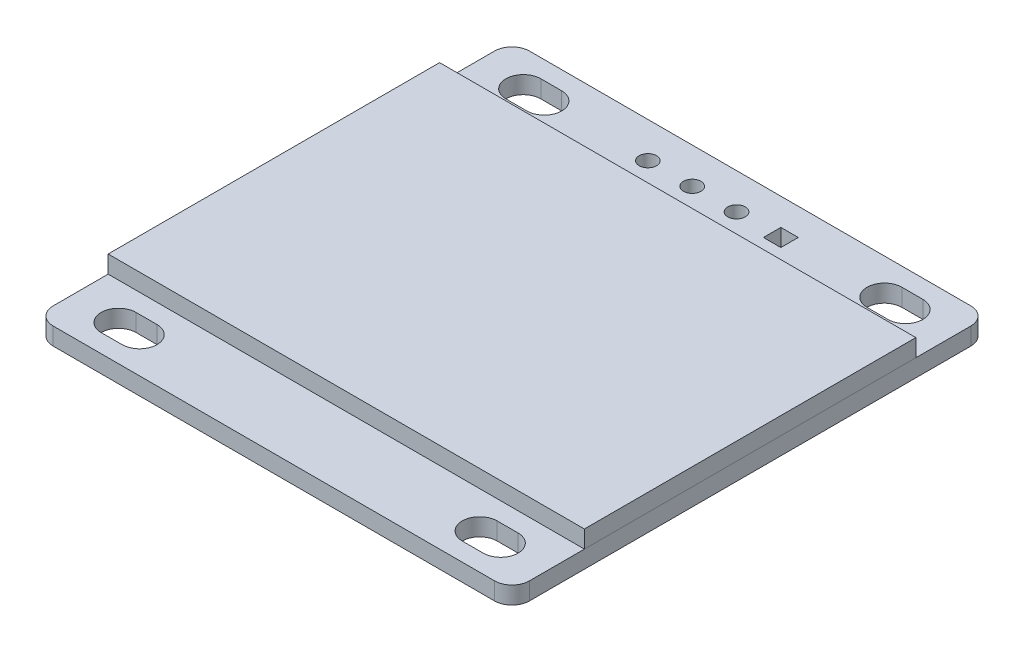
SolidWorks part; units mm, degrees
ref_plane "Přední rovina" through (0, 0, 0) normal (0, 0, 1) x (1, 0, 0)
ref_plane "Vrchní rovina" through (0, 0, 0) normal (0, 1, 0) x (1, 0, 0)
ref_plane "Pravá rovina" through (0, 0, 0) normal (1, 0, 0) x (0, 0, -1)
sketch "Skica1" plane through (0, 0, 0) normal (0, 1, 0) x (1, 0, 0)
  line L1 (0, 0) -> (27.3, 0)
  line L2 (0, 0) -> (0, 27.3)
  line L3 (0, 27.3) -> (27.3, 27.3)
  line L4 (27.3, 0) -> (27.3, 27.3)
  dimension "D1" = 27.3
  dimension "D2" = 27.3
extrude "Přidat vysunutím1" add sketch "Skica1" along normal blind 1
sketch "Skica2" plane through (0, 1, 0) normal (0, 1, 0) x (1, 0, 0)
  line L0 (0, 13.65) -> (27.3, 13.65) construction
  line L1 (0, 27.3) -> (0, 0) construction
  line L2 (27.3, 0) -> (27.3, 27.3) construction
  line L4 (0, 4.15) -> (27.3, 4.15)
  line L5 (0, 4.15) -> (0, 23.15)
  line L6 (0, 23.15) -> (27.3, 23.15)
  line L7 (27.3, 4.15) -> (27.3, 23.15)
  line L8 (0, 4.15) -> (27.3, 23.15) construction
  line L9 (0, 23.15) -> (27.3, 4.15) construction
  point P6 (13.65, 13.65)
  dimension "D1" = 19
extrude "Přidat vysunutím2" add sketch "Skica2" along normal blind 1 separate body
sketch "Skica3" plane through (0, 1, 0) normal (0, 1, 0) x (1, 0, 0)
  line L0 (0, 13.65) -> (27.3, 13.65) construction
  line L1 (0, 27.3) -> (0, 0) construction
  line L2 (27.3, 4.15) -> (27.3, 23.15) construction
  line L3 (13.65, 27.3) -> (13.65, 0) construction
  line L4 (27.3, 27.3) -> (0, 27.3) construction
  line L5 (0, 0) -> (27.3, 0) construction
  line L6 (0, 25.25) -> (27.3, 25.25) construction
  line L7 (27.3, 0) -> (27.3, 27.3) construction
  line L8 (3.3, 27.3) -> (3.3, 23.15) construction
  line L9 (27.3, 23.15) -> (0, 23.15) construction
  line L10 (2.7, 25.25) -> (3.9, 25.25) construction
  line L11 (2.7, 26.25) -> (3.9, 26.25)
  line L12 (2.7, 24.25) -> (3.9, 24.25)
  line L13 (24.6, 25.25) -> (23.4, 25.25) construction
  line L14 (24.6, 26.25) -> (23.4, 26.25)
  line L15 (24.6, 24.25) -> (23.4, 24.25)
  line L16 (2.7, 2.05) -> (3.9, 2.05) construction
  line L17 (2.7, 1.05) -> (3.9, 1.05)
  line L18 (2.7, 3.05) -> (3.9, 3.05)
  line L19 (24.6, 2.05) -> (23.4, 2.05) construction
  line L20 (24.6, 1.05) -> (23.4, 1.05)
  line L21 (24.6, 3.05) -> (23.4, 3.05)
  line L23 (16.96, 24.75) -> (17.96, 24.75)
  line L24 (16.96, 24.75) -> (16.96, 25.75)
  line L25 (16.96, 25.75) -> (17.96, 25.75)
  line L26 (17.96, 24.75) -> (17.96, 25.75)
  line L27 (16.96, 24.75) -> (17.96, 25.75) construction
  line L28 (16.96, 25.75) -> (17.96, 24.75) construction
  arc A0 (2.7, 26.25) -> (2.7, 24.25) centre (2.7, 25.25) ccw
  arc A1 (3.9, 24.25) -> (3.9, 26.25) centre (3.9, 25.25) ccw
  arc A2 (24.6, 26.25) -> (24.6, 24.25) centre (24.6, 25.25) cw
  arc A3 (23.4, 24.25) -> (23.4, 26.25) centre (23.4, 25.25) cw
  arc A4 (2.7, 1.05) -> (2.7, 3.05) centre (2.7, 2.05) cw
  arc A5 (3.9, 3.05) -> (3.9, 1.05) centre (3.9, 2.05) cw
  arc A6 (24.6, 1.05) -> (24.6, 3.05) centre (24.6, 2.05) ccw
  arc A7 (23.4, 3.05) -> (23.4, 1.05) centre (23.4, 2.05) ccw
  circle A8 centre (9.84, 25.25) radius 0.5
  circle A9 centre (12.38, 25.25) radius 0.5
  circle A10 centre (14.92, 25.25) radius 0.5
  point P22 (3.3, 25.25)
  point P31 (17.46, 25.25)
  point P36 (24, 25.25)
  point P43 (3.3, 2.05)
  point P50 (24, 2.05)
  point P57 (0, 0)
  dimension "D3" = 3.2
  dimension "D1" = 11.6
  dimension "D2" = 10.35
  dimension "D4" = 2
  dimension "D5" = 2.54
  dimension "D6" = 2.54
  dimension "D7" = 2.54
  dimension "D8" = 1
fillet "Zaoblit1" radius 1 4 edges at (0, 0.5, 0) (27.3, 0.5, 0) (27.3, 0.5, -27.3) (0, 0.5, -27.3)
extrude "Odebrat vysunutím1" cut sketch "Skica3" against normal up to next (1 mm away)
